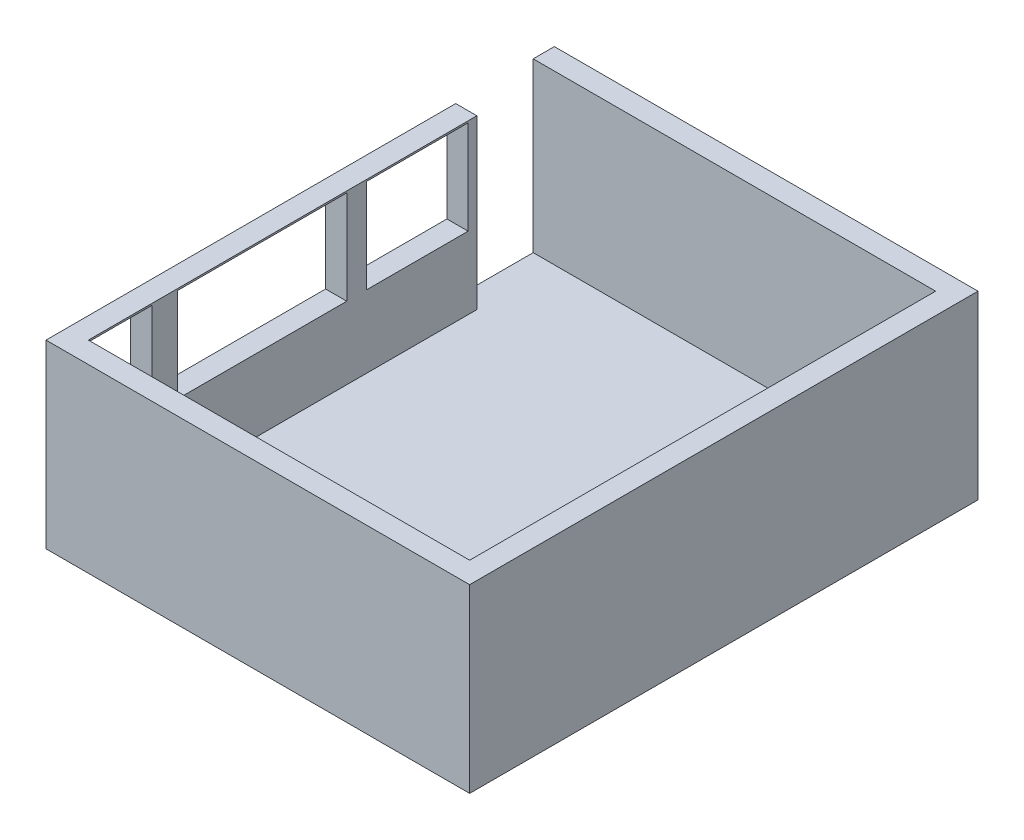
SolidWorks part; units mm, degrees
ref_plane "Front Plane" through (0, 0, 0) normal (0, 0, 1) x (1, 0, 0)
ref_plane "Top Plane" through (0, 0, 0) normal (0, 1, 0) x (1, 0, 0)
ref_plane "Right Plane" through (0, 0, 0) normal (1, 0, 0) x (0, 0, -1)
sketch "Sketch2" plane through (0, 0, 0) normal (0, 1, 0) x (1, 0, 0)
  line L0 (-4876.3323, 28.8884) -> (-4876.3323, -5971.1116)
  line L1 (-4876.3323, -5971.1116) -> (123.6677, -5971.1116)
  line L2 (123.6677, -5971.1116) -> (123.6677, 28.8884)
  line L3 (123.6677, 28.8884) -> (-4876.3323, 28.8884)
  dimension "D1" = 5000
  dimension "D2" = 6000
extrude "Boss-Extrude1" add sketch "Sketch2" along normal blind 2133.6 contours L2 L3 L0 L1
sketch "Sketch3" plane through (0, 2133.6, 0) normal (0, 1, 0) x (1, 0, 0)
  line L0 (-4626.3323, -221.1116) -> (-4626.3323, -5721.1116)
  line L1 (123.6677, 28.8884) -> (-4876.3323, 28.8884) construction
  line L2 (-4876.3323, -5971.1116) -> (123.6677, -5971.1116) construction
  line L3 (-126.3323, -221.1116) -> (-126.3323, -5721.1116)
  line L4 (-4876.3323, 28.8884) -> (-4876.3323, -5971.1116) construction
  line L5 (123.6677, -5971.1116) -> (123.6677, 28.8884) construction
  line L6 (-4626.3323, -5721.1116) -> (-126.3323, -5721.1116)
  line L7 (-4626.3323, -221.1116) -> (-126.3323, -221.1116)
  dimension "D1" = 250
  dimension "D2" = 250
  dimension "D3" = 250
  dimension "D4" = 250
extrude "Wall" cut sketch "Sketch3" against normal blind 1981.2
sketch "Sketch4" plane through (-4876.3323, 0, 0) normal (-1, 0, 0) x (0, 0, 1)
  line L0 (221.1116, 152.4) -> (221.1116, 2133.6)
  line L1 (-28.8884, 0) -> (5971.1116, 0) construction
  line L2 (-28.8884, 2133.6) -> (5971.1116, 2133.6) construction
  line L3 (221.1116, 2133.6) -> (1135.5116, 2133.6)
  line L4 (1135.5116, 2133.6) -> (1135.5116, 152.4)
  line L5 (-28.8884, 2133.6) -> (-28.8884, 0) construction
  line L6 (221.1116, 152.4) -> (1135.5116, 152.4)
  dimension "D1" = 250
  dimension "D2" = 914.4
  dimension "D3" = 152.4
sketch "Sketch5" plane through (-4626.3323, 0, 0) normal (1, 0, 0) x (0, 0, -1)
  line L0 (-1239.1314, 2113.5218) -> (-1239.1314, 1005.84)
  line L2 (-1239.1314, 1005.84) -> (-2439.1314, 1005.84)
  line L3 (-5971.1116, 2133.6) -> (-5971.1116, 0) construction
  line L4 (-5721.1116, 2113.5218) -> (-5721.1116, 1005.84)
  line L5 (-4971.1116, 2113.5218) -> (-4971.1116, 1005.84)
  line L6 (-2671.1116, 2113.5218) -> (-2671.1116, 1005.84)
  line L7 (-2439.1314, 2113.5218) -> (-2439.1314, 1005.84)
  line L8 (-4671.1116, 2113.5218) -> (-4671.1116, 1005.84)
  line L9 (-2671.1116, 1005.84) -> (-4671.1116, 1005.84)
  line L10 (-4971.1116, 1005.84) -> (-5721.1116, 1005.84)
  line L11 (-5721.1116, 2113.5218) -> (-4971.1116, 2113.5218)
  line L12 (-4671.1116, 2113.5218) -> (-2671.1116, 2113.5218)
  line L13 (-2439.1314, 2113.5218) -> (-1239.1314, 2113.5218)
  dimension "D1" = 250
  dimension "D2" = 750
  dimension "D3" = 2000
  dimension "D4" = 300
  dimension "D5" = 1200
extrude "Door" cut sketch "Sketch5" against normal blind 250
extrude "Windows" cut sketch "Sketch4" against normal blind 250
